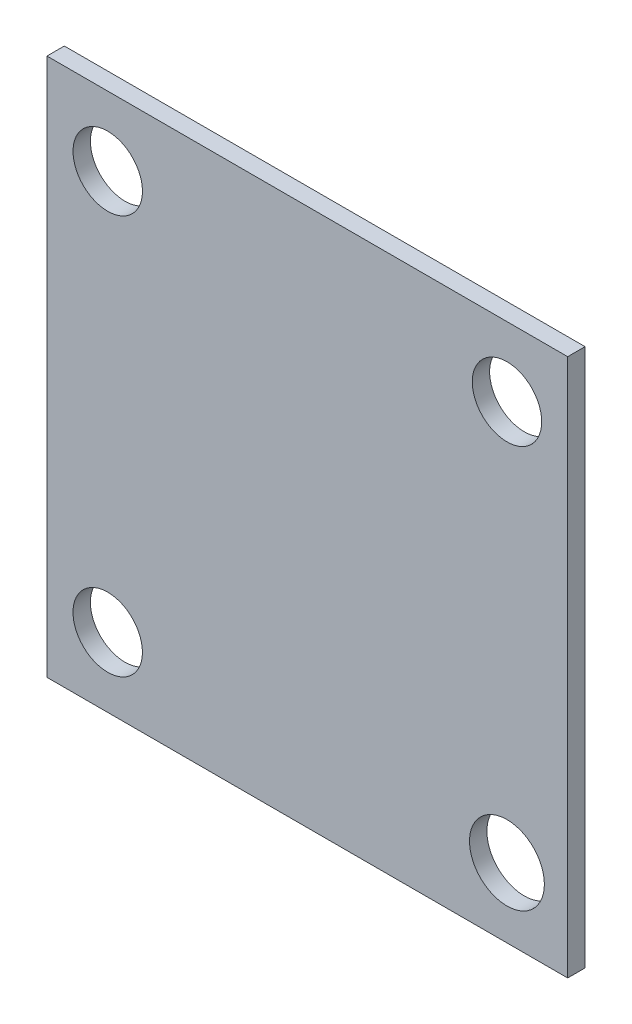
SolidWorks part; units mm, degrees
ref_plane "Front Plane" through (0, 0, 0) normal (0, 0, 1) x (1, 0, 0)
ref_plane "Top Plane" through (0, 0, 0) normal (0, 1, 0) x (1, 0, 0)
ref_plane "Right Plane" through (0, 0, 0) normal (1, 0, 0) x (0, 0, -1)
sketch "Sketch2" plane through (0, 0, 0) normal (0, 0, 1) x (1, 0, 0)
  line L0 (15.0011, -15.5011) -> (-15.0011, -15.5011)
  line L1 (15.0011, -15.5011) -> (15.0011, 15.5011)
  line L2 (15.0011, 15.5011) -> (-15.0011, 15.5011)
  line L3 (-15.0011, -15.5011) -> (-15.0011, 15.5011)
  circle A0 centre (-11.4989, 11.5033) radius 2
  circle A1 centre (11.5033, 11.5011) radius 2
  circle A2 centre (-11.5011, -11.4989) radius 2
  circle A3 centre (11.5011, -11.5011) radius 2.1563
  dimension "D1" = 4
  dimension "D2" = 4
  dimension "D3" = 4
  dimension "D4" = 4.3125
extrude "Boss-Extrude1" add sketch "Sketch2" along normal blind 1
